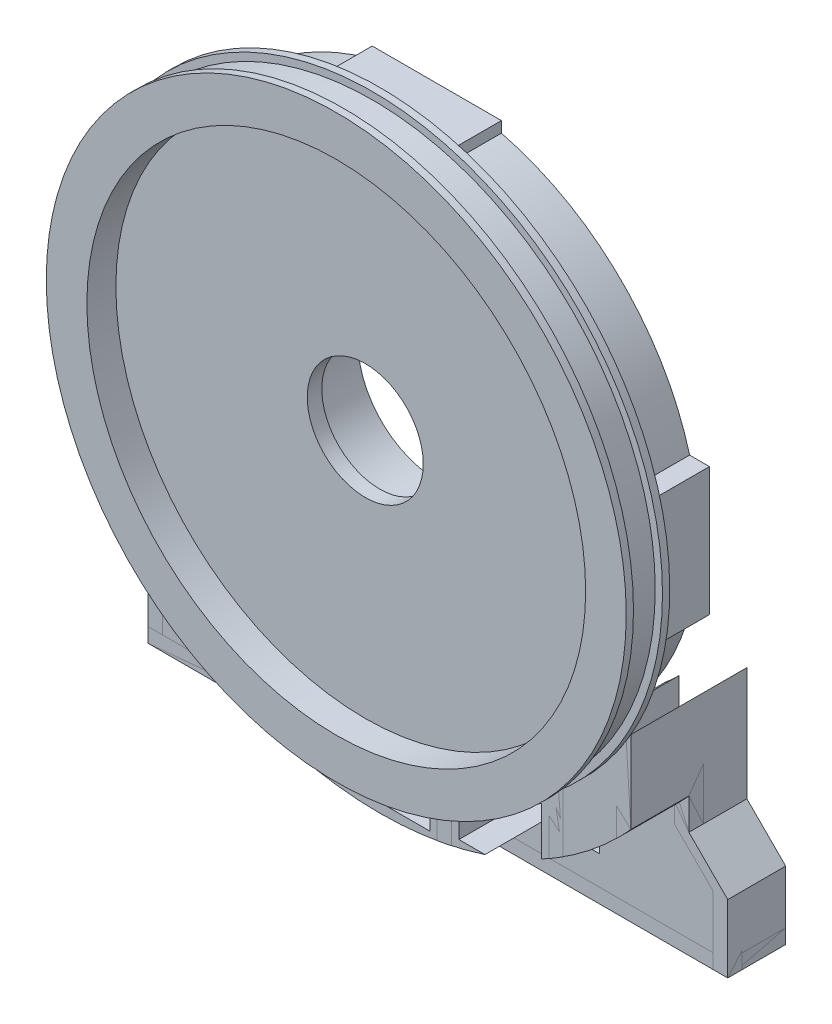
SolidWorks part; units mm, degrees
ref_plane "Front Plane" through (0, 0, 0) normal (0, 0, 1) x (1, 0, 0)
ref_plane "Top Plane" through (0, 0, 0) normal (0, 1, 0) x (1, 0, 0)
ref_plane "Right Plane" through (0, 0, 0) normal (1, 0, 0) x (0, 0, -1)
sketch "Sketch1" plane through (0, 0, 0) normal (0, 0, 1) x (1, 0, 0)
  circle A0 centre (0, 0) radius 200
extrude "Boss-Extrude1" add sketch "Sketch1" along normal blind 5
sketch "Sketch2" plane through (0, 0, 5) normal (0, 0, 1) x (1, 0, 0)
  circle A0 centre (0, 0) radius 195
extrude "Boss-Extrude2" add sketch "Sketch2" along normal blind 10
ref_plane "Plane1" through (0, 0, 15) normal (0, 0, 1) x (1, 0, 0)
mirror "Mirror2" about plane through (0, 0, 15) normal (0, 0, 1) of "Boss-Extrude2", "Boss-Extrude1"
mirror "Mirror3" about plane through (0, 0, 15) normal (0, 0, 1) of "Boss-Extrude1"
sketch "Sketch4" plane through (0, 0, 0) normal (0, 0, 1) x (1, 0, 0)
  circle A0 centre (0, 0) radius 180
  circle A1 centre (0, 0) radius 172
extrude "Boss-Extrude3" add sketch "Sketch4" against normal blind 40
sketch "Sketch5" plane through (0, 0, 0) normal (0, 0, -1) x (-1, 0, 0)
  circle A0 centre (0, 0) radius 104.5
  circle A1 centre (0, 0) radius 96.5
sketch "Sketch6" plane through (0, 0, 0) normal (0, 0, -1) x (-1, 0, 0)
  circle A0 centre (0, 0) radius 40
extrude "Cut-Extrude1" cut sketch "Sketch6" against normal through all both and the other way through all
sketch "Sketch7" plane through (0, 0, 30) normal (0, 0, 1) x (1, 0, 0)
  circle A0 centre (0, 0) radius 172
  circle A1 centre (0, 0) radius 40 construction
extrude "Cut-Extrude2" cut sketch "Sketch7" against normal blind 20
sketch "Sketch8" plane through (0, 0, 0) normal (0, 0, -1) x (-1, 0, 0)
  line L1 (-226.8867, 0) -> (327.5333, 0) construction
  line L3 (10.3528, -38.637) -> (44.5169, -166.1392) construction
sketch "Sketch11" plane through (0, 0, 0) normal (0, 0, -1) x (-1, 0, 0)
  line L0 (0, 220.657) -> (0, -234.2087) construction
  line L1 (10.3528, -38.637) -> (44.5169, -166.1392) construction
  line L3 (13.739, -37.0329) -> (48.7398, -168.4842) construction
  line L6 (41.8584, -170.3245) -> (7.0358, -38.9499) construction
  line L8 (7.0358, -38.9499) -> (13.739, -37.0329)
  line L9 (7.0358, -38.9499) -> (41.8584, -170.3245)
  line L10 (13.739, -37.0329) -> (48.7398, -168.4842)
  line L11 (41.8584, -170.3245) -> (48.7398, -168.4842)
  dimension "D1" = 15
extrude "Boss-Extrude12" add sketch "Sketch11" along normal blind 40
pattern_circular "CirPattern7" count 12 every 30 about axis through (0, 0, 0) along (0, 0, 1) of "Boss-Extrude12"
extrude "Boss-Extrude14" add sketch "Sketch5" along normal blind 40
sketch "Sketch16" plane through (0, 0, 0) normal (0, 0, -1) x (-1, 0, 0)
  circle A0 centre (0, 0) radius 63
  circle A2 centre (0, 0) radius 55
extrude "Boss-Extrude15" add sketch "Sketch16" along normal blind 40
sketch "Sketch17" plane through (0, 0, 0) normal (0, 0, -1) x (-1, 0, 0)
  circle A0 centre (0, 0) radius 55
  circle A1 centre (0, 0) radius 40
ref_plane "Plane3" through (0, 0, -40) normal (0, 0, -1) x (-1, 0, 0)
sketch "Sketch18" plane through (0, 0, -40) normal (0, 0, -1) x (-1, 0, 0)
  circle A1 centre (0, 0) radius 55
extrude "Cut-Extrude9" cut sketch "Sketch18" against normal blind 40
sketch "Sketch20" plane through (0, 0, 0) normal (0, 0, -1) x (-1, 0, 0)
  line L0 (-76.3832, 71.3152) -> (-124.0564, 119.1386)
  line L1 (76.2988, 71.4055) -> (124.1704, 119.0198)
  line L2 (-70.7313, 65.6455) -> (-47.0532, 41.8927)
  line L3 (70.6239, 65.7611) -> (46.8523, 42.1173)
  arc A0 (76.2988, 71.4055) -> (-76.3832, 71.3152) centre (0, 0) ccw
  arc A1 (124.1704, 119.0198) -> (-124.0564, 119.1386) centre (0, 0) ccw
  arc A2 (46.8523, 42.1173) -> (-47.0532, 41.8927) centre (0, 0) ccw
  arc A3 (70.6239, 65.7611) -> (-70.7313, 65.6455) centre (0, 0) ccw
extrude "Cut-Extrude13" cut sketch "Sketch20" along normal blind 40
sketch "Sketch21" plane through (0, 0, -40) normal (0, 0, -1) x (-1, 0, 0)
  line L0 (0, 245.7288) -> (0, -237.5415) construction
  line L1 (-138.1613, 239.3024) -> (0, 0) construction
  line L2 (0, 0) -> (159.1654, 275.6826) construction
  line L3 (-33.0054, 0) -> (-33.0054, 111.1117) construction
  dimension "D1" = 30
  dimension "D2" = 60
sketch "Sketch22" plane through (0, 0, -40) normal (0, 0, -1) x (-1, 0, 0)
  line L0 (25.0054, 0) -> (25.0054, 281.7628) construction
  line L1 (-25.0054, 0) -> (-25.0054, 250.3344) construction
  line L2 (-33.0054, 0) -> (-33.0054, 111.1117) construction
  line L3 (33.0054, 0) -> (33.0054, 272.1332) construction
  line L4 (-33.0054, 0) -> (-33.0054, 250.3344) construction
  point P11 (-25.0054, 48.987)
  point P12 (-513.0578, 150.8351)
  dimension "D1" = 8
sketch "Sketch25" plane through (0, 0, -40) normal (0, 0, -1) x (-1, 0, 0)
  line L0 (-30.0323, 46.0767) -> (-30.0323, 76.987)
  line L1 (-38.0323, 39.7309) -> (-38.0323, 76.987)
  line L2 (-38.0323, 76.987) -> (38, 76.987)
  line L3 (30, 46.0977) -> (30, 76.987)
  line L4 (-38, 66.987) -> (38, 66.987)
  line L8 (38, 39.7618) -> (38, 76.987)
  line L10 (-30.0323, 176.987) -> (-30.0323, 177.4769)
  line L12 (0, 245.7288) -> (0, -237.5415) construction
  line L13 (0, 130) -> (-38.0323, 130)
  line L16 (38, 130) -> (0, 130)
  line L20 (-38.0323, 76.987) -> (-38.0323, 175.9362)
  line L21 (38, 76.987) -> (38, 175.9432)
  line L22 (30, 76.987) -> (30, 177.4824)
  line L25 (-30.0323, 76.987) -> (-30.0323, 176.987)
  line L26 (-38.0323, 122) -> (38, 122)
  arc A0 (38, 175.9432) -> (-38.0323, 175.9362) centre (0, 0) ccw
  arc A1 (38, 39.7618) -> (30, 46.0977) centre (0, 0) ccw
  arc A2 (-30.0323, 46.0767) -> (-38.0323, 39.7309) centre (0, 0) ccw
  dimension "D1" = 8
  dimension "D4" = 8
  dimension "D2" = 8
extrude "Boss-Extrude18" add sketch "Sketch25" against normal blind 40
sketch "Sketch27" plane through (0, 0, 0) normal (0, 0, -1) x (-1, 0, 0)
  line L1 (-30.0323, 122) -> (30, 122)
  line L2 (-30.0323, 122) -> (-30.0323, 76.987)
  line L3 (-30.0323, 76.987) -> (30, 76.987)
  line L4 (30, 122) -> (30, 76.987)
  line L5 (-30.0323, 122) -> (30, 76.987) construction
  line L6 (-30.0323, 76.987) -> (30, 122) construction
  line L7 (-30.0323, 66.987) -> (30, 66.987)
  line L8 (-30.0323, 66.987) -> (-30.0323, 40)
  line L9 (-30.0323, 40) -> (30, 40)
  line L10 (30, 66.987) -> (30, 40)
  line L11 (-30.0323, 66.987) -> (30, 40) construction
  line L12 (-30.0323, 40) -> (30, 66.987) construction
  point P4 (-0.0161, 99.4935)
  point P11 (-0.0161, 53.4935)
extrude "Cut-Extrude15" cut sketch "Sketch27" along normal blind 40
ref_plane "Plane4" through (0, 0, -50) normal (0, 0, -1) x (-1, 0, 0)
sketch "Sketch30" plane through (0, 0, -50) normal (0, 0, -1) x (-1, 0, 0)
  line L0 (-38.0323, 97.3334) -> (-38.0323, 167.7425) construction
  line L1 (-38.0323, 130) -> (38, 130)
  line L2 (-38.0323, 130) -> (-38.0323, 167.7425)
  line L4 (38, 130) -> (38, 167.7498)
  arc A0 (38, 167.7498) -> (-38.0323, 167.7425) centre (0, 0) ccw
  point P4 (-0.0161, 151.6509)
extrude "Cut-Extrude16" cut sketch "Sketch30" against normal blind 35
ref_plane "Plane5" through (0, 0, -40) normal (0, 0, -1) x (-1, 0, 0)
sketch "Sketch31" plane through (0, 0, -40) normal (0, 0, -1) x (-1, 0, 0)
  line L0 (-38.0323, 167.7425) -> (-38.0323, 182.0805)
  line L1 (-43.8991, 172.6431) -> (-43.8991, 166.3035)
  line L2 (38, 182.0805) -> (38, 167.7498)
  line L3 (-43.8991, 182.0805) -> (45.1952, 182.0805)
  line L8 (-43.8991, 182.0805) -> (-43.8991, 172.6431)
  line L9 (-43.8991, 172.6431) -> (45.1952, 172.6431)
  line L10 (45.1952, 182.0805) -> (45.1952, 172.6431)
  line L11 (45.1952, 172.6431) -> (45.1952, 165.956)
  arc A0 (45.1952, 165.956) -> (-43.8991, 166.3035) centre (0, 0) ccw
  point P10 (-0.0193, 178.6973)
  point P11 (0.648, 177.3618)
extrude "Boss-Extrude19" add sketch "Sketch31" against normal blind 44 contours A0 L0 L9 L1 | L8 L9 L0 L3 | L0 L9 L2 L3 | A0 L2 L9 L0 | A0 L11 L9 L2 | L10 L3 L2 L9
sketch "Sketch32" plane through (0, 0, 0) normal (0, 0, 1) x (1, 0, 0)
  line L0 (0, 0) -> (-173.1406, -99.4798)
  line L1 (0, 0) -> (0, -390) construction
  line L2 (0, 0) -> (173.1482, -99.4666)
  line L3 (173.1482, -99.4666) -> (173.1482, -389.8428)
  line L4 (-173.1406, -99.4798) -> (-173.1406, -389.8428)
  line L5 (0.0076, -199.6845) -> (0, -390)
  line L6 (173.1482, -389.8428) -> (-173.1406, -389.8428)
  line L12 (125.8692, -389.8428) -> (126.5384, -128.0157)
  line L14 (39.5868, -389.8428) -> (39.5868, -195.7212)
  line L16 (49.5868, -389.8428) -> (49.5868, -173.0351)
  line L17 (39.5868, -389.8428) -> (39.5868, -175.593)
  line L19 (-39.4279, -389.8428) -> (-39.4279, -175.6287)
  line L21 (-49.4279, -389.8428) -> (-49.4279, -173.0806)
  line L24 (-116.5381, -389.8428) -> (-116.5381, -137.1819)
  line L26 (-126.5381, -389.8428) -> (-126.5381, -128.016)
  line L28 (116.0868, -389.8428) -> (116.733, -137.0161)
  arc A0 (-173.1406, -99.4798) -> (173.1482, -99.4666) centre (0, 0) ccw
  circle A1 centre (0, 0) radius 180
  point P15 (173.1482, -99.4666)
  point P16 (-173.1406, -99.4798)
extrude "Boss-Extrude20" add sketch "Sketch32" against normal blind 80 contours A0 L28 L6 L12 | A1 L28 A0 L12 | A1 L17 A0 L16 | A0 L14 L6 L16 | A1 L21 A0 L19 | A0 L21 L6 L19 | A1 L26 A0 L24 | A0 L26 L6 L24
sketch "Sketch33" plane through (0, 0, 0) normal (0, 0, -1) x (-1, 0, 0)
  line L2 (0, 0) -> (0, -342.4917) construction
  line L3 (-173.2051, -100) -> (-173.2051, -178.3656)
  line L5 (173.2051, -100) -> (173.2051, -178.6485)
  line L6 (190, -389.8428) -> (190, -205.4434)
  line L7 (-200, -205.1605) -> (-200, -389.8428)
  line L8 (200, -205.4434) -> (200, -389.8428)
  line L9 (-173.2051, -178.3656) -> (-200, -205.1605)
  line L10 (173.2051, -178.6485) -> (200, -205.4434)
  line L13 (190, -389.8428) -> (200, -389.8428)
  line L15 (-190, -389.8428) -> (-190, -205.1605)
  line L16 (-190, -205.1605) -> (-163.2051, -178.3656)
  line L17 (-163.2051, -178.3656) -> (-163.2051, -115.6032)
  line L19 (-190, -389.8428) -> (-200, -389.8428)
  line L20 (190, -205.4434) -> (163.2051, -178.6485)
  line L21 (163.2051, -178.6485) -> (163.2051, -115.6032)
  line L22 (-190, -389.8428) -> (190, -389.8428)
  arc A0 (-173.2051, -100) -> (173.2051, -100) centre (0, 0) ccw
extrude "Boss-Extrude21" add sketch "Sketch33" along normal blind 80 separate body contours A0 L3 L9 L7 L19 L15 L16 L17 | A0 L21 L20 L6 L13 L8 L10 L5
sketch "Sketch34" plane through (0, 0, 0) normal (0, 0, -1) x (-1, 0, 0)
  line L0 (-200, -389.8428) -> (200, -389.8428)
  line L1 (200, -389.8428) -> (200, -205.4434)
  line L2 (200, -205.4434) -> (173.2051, -178.6485)
  line L3 (173.2051, -178.6485) -> (173.2051, -100)
  line L4 (-200, -389.8428) -> (-200, -205.1605)
  line L5 (-200, -205.1605) -> (-173.2051, -178.3656)
  line L6 (-173.2051, -178.3656) -> (-173.2051, -100)
  circle A0 centre (0, 0) radius 200
  circle A1 centre (0, 0) radius 200
extrude "Boss-Extrude26" add sketch "Sketch34" along normal blind 50 separate body contours A0 L6 L5 L4 L0 L1 L2 L3
ref_plane "Plane8" through (0, 0, 0) normal (-1, 0, 0) x (0, 0, 1)
sketch "Sketch38" plane through (0, 0, 0) normal (-1, 0, 0) x (0, 0, 1)
  line L0 (0, -200) -> (197.9741, -200) construction
  line L1 (30, -200) -> (30, -304.3172) construction
  line L2 (30, -200) -> (0, -200) construction
  line L3 (0, -178.3656) -> (0, -205.1605) construction
  line L4 (0, -200) -> (0, -302.6251) construction
  line L5 (0, -205.1605) -> (0, -389.8428) construction
  line L6 (0, -200) -> (-40, -166.436) construction
  line L7 (-50, -205.1605) -> (-40, -205.1605) construction
  line L8 (-80, -205.1605) -> (0, -205.1605) construction
  line L9 (-40, -205.1605) -> (-40, -166.436) construction
  line L10 (0, 0) -> (-40, -166.436)
  line L11 (-40, -166.436) -> (-40, 0) construction
  line L13 (0, 0) -> (-40, 0) construction
  point P17 (-40, -166.436)
  dimension "D2" = 166.436
  dimension "D1" = 50
sketch "Sketch39" plane through (0, 0, 10) normal (0, 0, 1) x (1, 0, 0)
  line L0 (-233.56, 0) -> (-438.1523, 0)
  line L1 (233.56, 0) -> (438.1523, 0)
  arc A0 (-233.56, 0) -> (233.56, 0) centre (0, 0) ccw
  arc A1 (-438.1523, 0) -> (438.1523, 0) centre (0, 0) ccw
extrude "Cut-Extrude17" cut sketch "Sketch39" against normal blind 40
ref_plane "Plane9" through (0, 0, 30) normal (0, 0, 1) x (1, 0, 0)
sketch "Sketch41" plane through (0, 0, 30) normal (0, 0, 1) x (1, 0, 0)
  line L0 (-306.4353, 0) -> (417.3108, 0) construction
  line L1 (0, 247.8182) -> (0, -475.0549) construction
  line L2 (0, -172) -> (470.7399, -172) construction
  line L3 (470.7399, -172) -> (-364.2612, -172) construction
  line L4 (0, -172) -> (0, -252) construction
  line L5 (-200, -389.8428) -> (200, -389.8428)
  line L6 (-200, -389.8428) -> (-200, -252)
  line L7 (200, -389.8428) -> (200, -252)
  line L8 (-200, -252) -> (200, -252)
  circle A0 centre (0, 0) radius 172 construction
  dimension "D1" = 0
extrude "Cut-Extrude18" cut sketch "Sketch41" against normal through all
sketch "Sketch42" plane through (0, 0, -40) normal (0, 0, -1) x (-1, 0, 0)
  line L0 (200, -252) -> (-200, -252)
  line L1 (200, -252) -> (200, -242)
  line L2 (-200, -252) -> (-200, -242)
  line L3 (200, -242) -> (-200, -242)
extrude "Boss-Extrude29" add sketch "Sketch42" along normal blind 40 and the other way blind 10 separate body
ref_plane "Plane10" through (0, 0, 0) normal (0, 0, -1) x (-1, 0, 0)
sketch "Sketch43" plane through (0, 0, 0) normal (0, 0, -1) x (-1, 0, 0)
  line L0 (-291.6105, 0) -> (344.5212, 0) construction
  line L1 (0, 0) -> (-368.629, 6.4344) construction
  line L2 (0, 0) -> (351.9144, 43.2096) construction
  line L3 (198.5092, 24.3739) -> (175.9954, 207.734) construction
  line L4 (185.9984, 22.8377) -> (180.5142, 67.5023)
  line L5 (180.5142, 67.5023) -> (191.293, -20.2833)
  line L6 (180.5142, 67.5023) -> (163.235, 65.3807)
  line L10 (191.293, -20.2833) -> (172.6101, -22.5773)
  line L12 (-187.4012, 2.4048) -> (-187.4012, -41.2583)
  line L13 (-187.4012, -41.2583) -> (-187.4012, 47.1866)
  line L14 (-187.4012, -41.2583) -> (-169.9922, -41.2583)
  line L15 (-187.4012, 47.1866) -> (-168.5781, 47.1866)
  line L16 (0, 0) -> (-179.9726, 3.1414) construction
  arc A0 (163.235, 65.3807) -> (172.6101, -22.5773) centre (17.3203, 5.3496) cw
  arc A1 (-169.9922, -41.2583) -> (-168.5781, 47.1866) centre (-17.8492, 0.5428) cw
  arc A2 (-43.8991, 174.5648) -> (-126.5384, -128.0157) centre (0, 0) ccw construction
  point P20 (-175.61, 3.0653)
  dimension "D1" = 1
  dimension "D2" = 7
extrude "Boss-Extrude31" add sketch "Sketch43" along normal blind 40 contours L14 A1 L15 L13 L12 | L6 A0 L10 L5 L4
sketch "Sketch45" plane through (0, 0, -50) normal (0, 0, -1) x (-1, 0, 0)
  line L0 (205, -226.9042) -> (205, 0)
  line L1 (205, -237.3602) -> (205, -216.3758)
  line L2 (54.4279, -222) -> (111.5381, -222)
  line L3 (111.5381, -172.0007) -> (111.5381, -222)
  line L4 (54.4279, -197.6426) -> (54.4279, -222)
  line L5 (116.5381, -252) -> (116.5381, -137.1819) construction
  line L6 (49.4279, -252) -> (49.4279, -173.0806) construction
  line L7 (200, -242) -> (-200, -242) construction
  line L8 (-39.5868, -252) -> (-39.5868, -175.593) construction
  line L10 (-34.5868, -202.0613) -> (-34.5868, -227)
  line L11 (-34.5868, -227) -> (34.4279, -227)
  line L12 (34.4279, -202.0884) -> (34.4279, -227)
  line L13 (39.4279, -252) -> (39.4279, -175.6287) construction
  line L14 (-49.5868, -252) -> (-49.5868, -173.0351) construction
  line L16 (-111.5158, -172.0152) -> (-111.5158, -222)
  line L17 (-111.5158, -222) -> (-54.5868, -222)
  line L18 (-54.5868, -197.5988) -> (-54.5868, -222)
  line L19 (-116.4391, -252) -> (-116.733, -137.0161) construction
  circle A0 centre (0, 0) radius 205
  dimension "D1" = 5
  dimension "D4" = 15
  dimension "D2" = 5
  dimension "D3" = 20
  dimension "D5" = 5
  dimension "D6" = 5
  dimension "D8" = 20
  dimension "D9" = 5
  dimension "D10" = 5
extrude "Cut-Extrude19" cut sketch "Sketch45" against normal through all contours A0 L10 L11 L12 | A0 L4 L2 L3 | A0 L16 L17 L18
sketch "Sketch48" plane through (0, 0, -30) normal (0, 0, 1) x (1, 0, 0)
  line L0 (-200, -252) -> (200, -252)
  line L1 (200, -252) -> (190, -252) construction
  line L2 (200, -252) -> (200, -155.8788)
  line L4 (200, -155.8788) -> (173.9312, -155.8788)
  line L5 (-200, -155.8788) -> (-200, -252)
  line L6 (-173.9312, -155.8788) -> (-200, -155.8788)
  arc A0 (-173.9312, -155.8788) -> (173.9312, -155.8788) centre (0, 0) ccw
extrude "Cut-Extrude20" cut sketch "Sketch48" against normal blind 10
sketch "Sketch49" plane through (0, 0, 10) normal (0, 0, 1) x (1, 0, 0)
  line L0 (0, 274.6736) -> (0, -309.1586) construction
  point P0 (0, 0)
ref_plane "Plane21" through (0, 0, 10) normal (0, -1, 0) x (-1, 0, 0)
